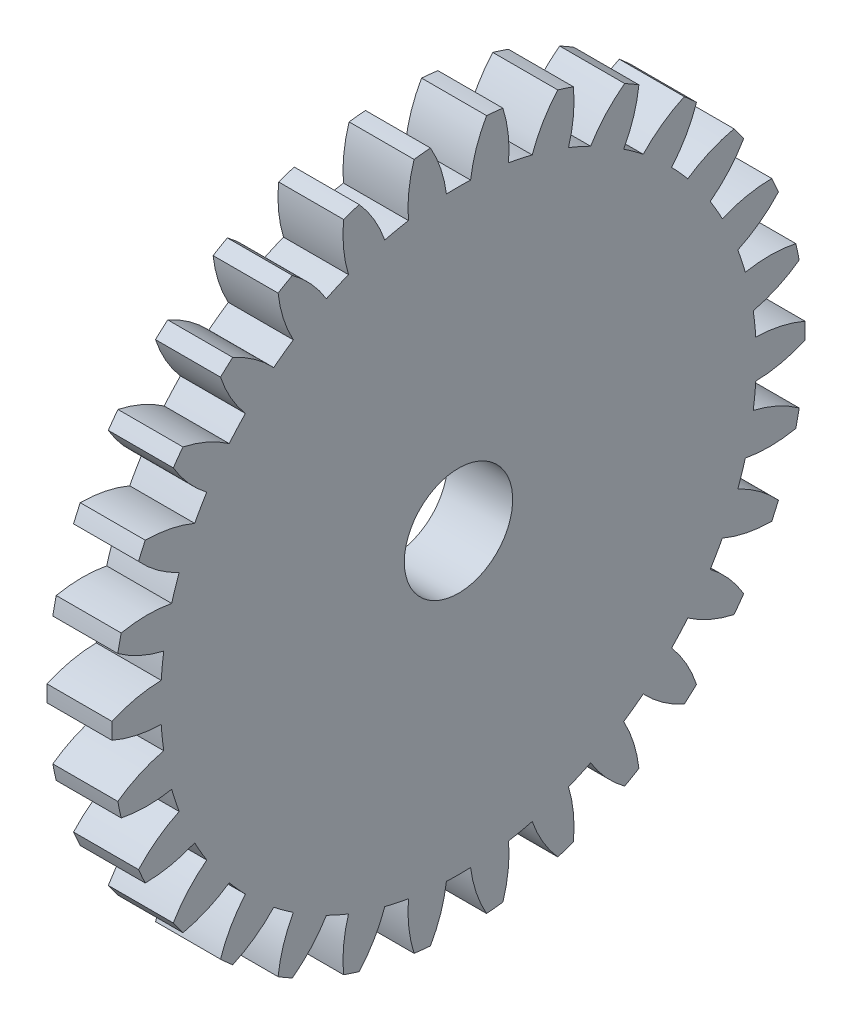
SolidWorks part; units mm, degrees
ref_plane "Plane1" through (0, 0, 0) normal (0, 0, 1) x (1, 0, 0)
ref_plane "Plane2" through (0, 0, 0) normal (0, 1, 0) x (1, 0, 0)
ref_plane "Plane3" through (0, 0, 0) normal (1, 0, 0) x (0, 0, -1)
sketch "HoldingSke" plane through (0, 0, 0) normal (0, 1, 0) x (1, 0, 0)
  line L0 (0, 0) -> (0.866, -0.5)
  line L1 (-15, 0) -> (100, 0) construction
  line L2 (0, 0) -> (-2.1039, 2.3779)
  line L3 (0, 0) -> (-11.863, 4.5341)
  line L4 (0, 0) -> (7.479, 4.318)
  line L5 (0, 0) -> (-46.8476, -17.4728)
  line L6 (0, 0) -> (-2.4869, -1.6779)
  line L7 (-2.1039, 2.3779) -> (8.6586, 51.2059)
  line L8 (-76.2, 54.61) -> (-75.3, 54.61)
  line L9 (-67.7845, 28.3722) -> (-49.3413, 33.142)
  line L10 (-76.2, 71.12) -> (104.1128, 71.12)
  line L11 (0, 0) -> (-3, 0)
  line L12 (-76.2, 101.6) -> (-76.162, 101.6)
  line L13 (24.9733, 27.94) -> (52.9518, 28.4284)
  line L14 (24.9733, 27.94) -> (24.9743, 27.94)
  line L15 (24.9733, 27.94) -> (100.4006, 29.5858)
  line L16 (-63.627, -1) -> (-12.827, -1)
  circle A0 centre (0, 0) radius 2.5
  circle A1 centre (0, 0) radius 13.749
  circle A2 centre (0, 0) radius 37.5
  circle A3 centre (0, 0) radius 2.5
  dimension "MHD" = 27.498
  dimension "Hub_dia" = 75
  dimension "Bore" = 5
  dimension "MBD" = 5
  dimension "Num_teeth" = 30
  dimension "Pitch_radius" = 180.3128
  dimension "Pitch" = 1
  dimension "Width" = 3
  dimension "Overall_len" = 50
  dimension "Show_teeth" = 30
  dimension "Thickness" = 3
  dimension "OAL" = 50.0001
  dimension "T_dim" = 0.9
  dimension "Ap" = 14.5
  dimension "H" = 19.05
  dimension "Backlash" = 0.038
  dimension "Addendum_fac" = 1
  dimension "Dedendum_fac" = 1.25
  dimension "Clearance_fac" = 0.25
  dimension "Dedendum_add" = 0.001
  dimension "Module" = 1
sketch "BasProSke" plane through (0, 0, 0) normal (0, 1, 0) x (1, 0, 0)
  line L0 (-10, 0) -> (60, 0) construction
  line L1 (0, 0) -> (0, 16)
  line L2 (0, 0) -> (3, 0)
  line L3 (3, 0) -> (3, 16)
  line L4 (3, 16) -> (0, 16)
  dimension "Diameter" = 32
  dimension "Thickness" = 3
revolve "Base-Revolve" add sketch "BasProSke" angle 360 about L0
sketch "TooCutSke" plane through (0, 0, 0) normal (1, 0, 0) x (0, 0, -1)
  line L1 (0, 0) -> (0, 107) construction
  line L2 (0, 0) -> (-0.8515, 14.9758) construction
  line L3 (0, 0) -> (-3.1323, 29.8014) construction
  line L4 (-0.8515, 14.9758) -> (-1.5661, 14.9007) construction
  arc A0 (0.5582, 13.7377) -> (-0.5582, 13.7377) centre (0, 0) ccw
  arc A1 (1.3088, 15.9719) -> (-1.3088, 15.9719) centre (0, 0) ccw
  circle A2 centre (0, 0) radius 15 construction
  circle A3 centre (0, 0) radius 14.5222 construction
  arc A4 (-0.5582, 13.7377) -> (-1.3088, 15.9719) centre (-6.5103, 12.9812) ccw
  arc A5 (1.3088, 15.9719) -> (0.5582, 13.7377) centre (6.5103, 12.9812) ccw
  dimension "Root_dia" = 27.498
  dimension "Overcut_dia" = 32.0508
  dimension "Pitch_dia" = 30
  dimension "Base_dia" = 29.0444
  dimension "Flank_rad" = 6
  dimension "Half_ang" = 6
  dimension "Half_CT" = 0.7185
extrude "ToothCut" cut sketch "TooCutSke" along normal through all
fillet "Breaks" [suppressed] radius 0.02
fillet "RootFillets" [suppressed] radius 0.251
pattern_circular "TeethCuts" count 30 every 12 about axis through (-10, 0, 0) along (1, 0, 0) of "ToothCut", "RootFillets", "Breaks"
sketch "HubNeaOneSke" plane through (0, 0, 0) normal (-1, 0, 0) x (0, 0, 1)
  circle A0 centre (0, 0) radius 13.749
  dimension "Diameter" = 27.498
extrude "HubNearOne" [suppressed] add sketch "HubNeaOneSke" along normal blind 47.0001
sketch "HubNeaBotSke" plane through (0, 0, 0) normal (-1, 0, 0) x (0, 0, 1)
  circle A0 centre (0, 0) radius 13.749
  dimension "Diameter" = 27.498
extrude "HubNearBoth" [suppressed] add sketch "HubNeaBotSke" along normal blind 23.5
ref_plane "FarPln" through (3, 0, 0) normal (1, 0, 0) x (0, 0, -1)
sketch "HubFarSke" plane through (3, 0, 0) normal (1, 0, 0) x (0, 0, -1)
  circle A0 centre (0, 0) radius 13.749
  dimension "Diameter" = 27.498
extrude "HubFar" [suppressed] add sketch "HubFarSke" along normal blind 23.5
sketch "BorSke" plane through (0, 0, 0) normal (1, 0, 0) x (0, 0, -1)
  circle A0 centre (0, 0) radius 2.5
  dimension "Diameter" = 5
extrude "Bore" cut sketch "BorSke" along normal mid plane 100.0001
sketch "KeySke" plane through (0, 0, 0) normal (1, 0, 0) x (0, 0, -1)
  line L0 (-1, 0) -> (-1, 3.4)
  line L1 (-1, 3.4) -> (1, 3.4)
  line L2 (1, 3.4) -> (1, 0)
  line L3 (0, 0) -> (0, 34) construction
  line L4 (-1, 0) -> (1, 0)
  dimension "Offset" = 3.4
  dimension "Width" = 2
extrude "Keyway" [suppressed] cut sketch "KeySke" along normal mid plane 100.0001
pattern_circular "Keyway2" [suppressed] count 2 every 90 about axis through (-10, 0, 0) along (1, 0, 0)
equation "' \"Module@HoldingSke\" = 6.35"
equation "' \"Num_teeth@HoldingSke\" = 12"
equation "' \"Ap@HoldingSke\" =  20"
equation "' \"Width@HoldingSke\" = 0.5 * 25.4"
equation "' \"Hub_dia@HoldingSke\"= 1 * 25.4"
equation "' \"Overall_len@HoldingSke\" = 1.0 * 25.4"
equation "' \"Bore@HoldingSke\" = 0.75 * 25.4"
equation "' \"T_dim@HoldingSke\" = 0.1 * 25.4"
equation "' \"Width@KeySke\" = 0.25 * 25.4"
equation "' \"Show_teeth@HoldingSke\" = 13"
equation "' \"Backlash@HoldingSke\" = 0.009 * 25.4"
equation "' \"Addendum_fac@HoldingSke\" = 1.0"
equation "' \"Dedendum_fac@HoldingSke\" = 1.25"
equation "' \"Dedendum_add@HoldingSke\" = 0.00005 * 25.4"
equation "' \"Clearance_fac@HoldingSke\" = 0.25"
equation "\"Pitch@HoldingSke\" = 1 / \"Module@HoldingSke\""
equation "\"Overcut_dia@TooCutSke\" = (\"Num_teeth@HoldingSke\" + 2 * \"Addendum_fac@HoldingSke\") / \"Pitch@HoldingSke\" + 0.002 * 25.4"
equation "\"Pitch_dia@TooCutSke\" = \"Num_teeth@HoldingSke\" / \"Pitch@HoldingSke\""
equation "\"Base_dia@TooCutSke\" = \"Num_teeth@HoldingSke\" / \"Pitch@HoldingSke\" * cos((\"Ap@HoldingSke\"  * 3.14159265 / 180))"
equation "\"Root_dia@TooCutSke\" = (\"Num_teeth@HoldingSke\" + 2) / \"Pitch@HoldingSke\" - 2 * (\"Addendum_fac@HoldingSke\" + \"Dedendum_fac@HoldingSke\") / \"Pitch@HoldingSke\" - \"Dedendum_add@HoldingSke\" * 2"
equation "\"Half_ang@TooCutSke\" = 180 / \"Num_teeth@HoldingSke\""
equation "\"Half_CT@TooCutSke\" = \"Num_teeth@HoldingSke\" / \"Pitch@HoldingSke\" * sin((3.14159265 / 2 / \"Num_teeth@HoldingSke\")) / 2 - 7 * \"Backlash@HoldingSke\" / 4"
equation "\"Flank_rad@TooCutSke\" = \"Num_teeth@HoldingSke\" / \"Pitch@HoldingSke\" / 5"
equation "\"Radius@RootFillets\" = \"Clearance_fac@HoldingSke\" / \"Pitch@HoldingSke\" + \"Dedendum_add@HoldingSke\""
equation "\"Break_rad@Breaks\" = 0.02 / \"Pitch@HoldingSke\""
equation "\"Thickness@HoldingSke\" = \"Width@HoldingSke\""
equation "\"OAL@HoldingSke\" = \"Thickness@HoldingSke\""
equation "\"MHD@HoldingSke\" = (\"Num_teeth@HoldingSke\" + 2) / \"Pitch@HoldingSke\" - 2 * (\"Addendum_fac@HoldingSke\" + \"Dedendum_fac@HoldingSke\")  / \"Pitch@HoldingSke\" - \"Dedendum_add@HoldingSke\" * 2"
equation "\"MBD@HoldingSke\" = (\"Num_teeth@HoldingSke\" + 2) / \"Pitch@HoldingSke\" - 2 * (\"Addendum_fac@HoldingSke\" + \"Dedendum_fac@HoldingSke\")  / \"Pitch@HoldingSke\" - \"Dedendum_add@HoldingSke\" * 2 - 0.002 * 25.4"
equation "\"MHD@HoldingSke\" = ((sgn( \"MHD@HoldingSke\" - \"Hub_dia@HoldingSke\" )-1)*( \"MHD@HoldingSke\" - \"Hub_dia@HoldingSke\" ))/-2+ \"Hub_dia@HoldingSke\""
equation "\"MBD@HoldingSke\" = ((sgn( \"MBD@HoldingSke\" - \"Bore@HoldingSke\" )-1)*( \"MBD@HoldingSke\" - \"Bore@HoldingSke\" ))/-2+ \"Bore@HoldingSke\""
equation "\"OAL@HoldingSke\" = ((sgn( \"OAL@HoldingSke\" - \"Overall_len@HoldingSke\" )+1)*( \"OAL@HoldingSke\" - \"Overall_len@HoldingSke\" ))/2 + \"Overall_len@HoldingSke\" + 0.000002 * 25.4"
equation "\"Num_teeth@TeethCuts\" = int( \"Show_teeth@HoldingSke\" ) + 1"
equation "\"Num_teeth@TeethCuts\" = ((sgn( \"Num_teeth@TeethCuts\" - \"Num_teeth@HoldingSke\" )-1)*( \"Num_teeth@TeethCuts\" - \"Num_teeth@HoldingSke\" ))/-2+ \"Num_teeth@HoldingSke\""
equation "\"Num_teeth@TeethCuts\" = ((sgn( \"Num_teeth@TeethCuts\" - 2.0)+1)*( \"Num_teeth@TeethCuts\" - 2.0))/2 +2.0"
equation "\"Angle@TeethCuts\" = 360.0 / \"Num_teeth@HoldingSke\""
equation "\"Diameter@BasProSke\" = (\"Num_teeth@HoldingSke\" + 2 * \"Addendum_fac@HoldingSke\") / \"Pitch@HoldingSke\""
equation "\"Thickness@BasProSke\"  = \"Thickness@HoldingSke\""
equation "' \"Fillet_rad@BasProSke\" =  \"Thickness@HoldingSke\" * 0.05"
equation "\"MHD@HoldingSke\" = ((sgn( \"MHD@HoldingSke\" - \"Root_dia@TooCutSke\" )-1)*( \"MHD@HoldingSke\" - \"Root_dia@TooCutSke\" ))/-2+ \"Root_dia@TooCutSke\""
equation "\"Diameter@HubNeaOneSke\" = \"MHD@HoldingSke\""
equation "\"Length@HubNearOne\" = \"OAL@HoldingSke\" - \"Thickness@BasProSke\""
equation "\"Diameter@HubNeaBotSke\" = \"MHD@HoldingSke\""
equation "\"Length@HubNearBoth\" = ( \"OAL@HoldingSke\" - \"Thickness@BasProSke\" ) / 2.0"
equation "\"Thickness@FarPln\" = \"Thickness@BasProSke\""
equation "\"Diameter@HubFarSke\" = \"MHD@HoldingSke\""
equation "\"Length@HubFar\" = ( \"OAL@HoldingSke\" - \"Thickness@BasProSke\" ) / 2.0"
equation "\"Diameter@BorSke\" = \"MBD@HoldingSke\""
equation "\"D1@Bore\" = \"OAL@HoldingSke\" * 2.0"
equation "\"D1@Keyway\" = \"OAL@HoldingSke\" * 2.0"
equation "\"Offset@KeySke\" = \"T_dim@HoldingSke\" + \"MBD@HoldingSke\" / 2.0"
